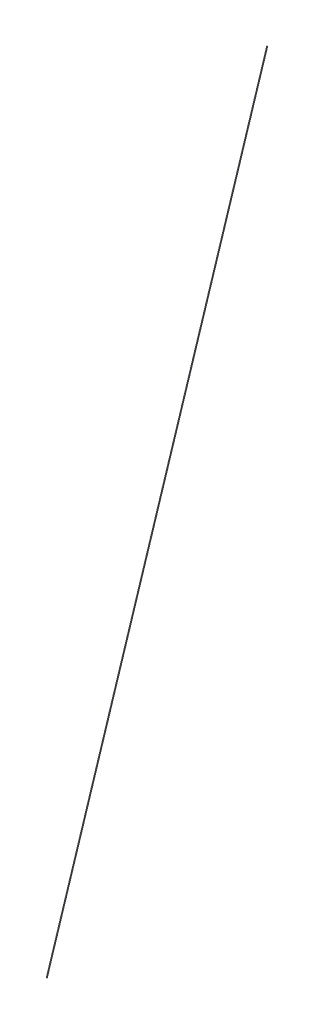
SolidWorks part; units mm, degrees
ref_plane "前视基准面" through (0, 0, 0) normal (0, 0, 1) x (1, 0, 0)
ref_plane "上视基准面" through (0, 0, 0) normal (0, 1, 0) x (1, 0, 0)
ref_plane "右视基准面" through (0, 0, 0) normal (1, 0, 0) x (0, 0, -1)
sketch "草图1" plane through (0, 0, 0) normal (0, 1, 0) x (1, 0, 0)
  line L0 (0, 0) -> (307.5, 0)
sketch "草图2" plane through (0, 0, 0) normal (0, 0, 1) x (1, 0, 0)
  line L0 (0, 0) -> (0, 1279.38)
sketch "草图3" plane through (0, 0, 0) normal (0, 0, 1) x (1, 0, 0)
  line L0 (307.5, 0) -> (0, 1279.38)
  line L1 (0, 0) -> (307.5, 0) construction
  line L2 (0, 1279.38) -> (307.5, 1279.38)
  line L3 (307.5, 1279.38) -> (307.5, 0)
  line L4 (0, 0) -> (307.5, 1279.38)
sweep "扫描1" add path "草图3" circular profile diameter 1 parameters "D3"=1
